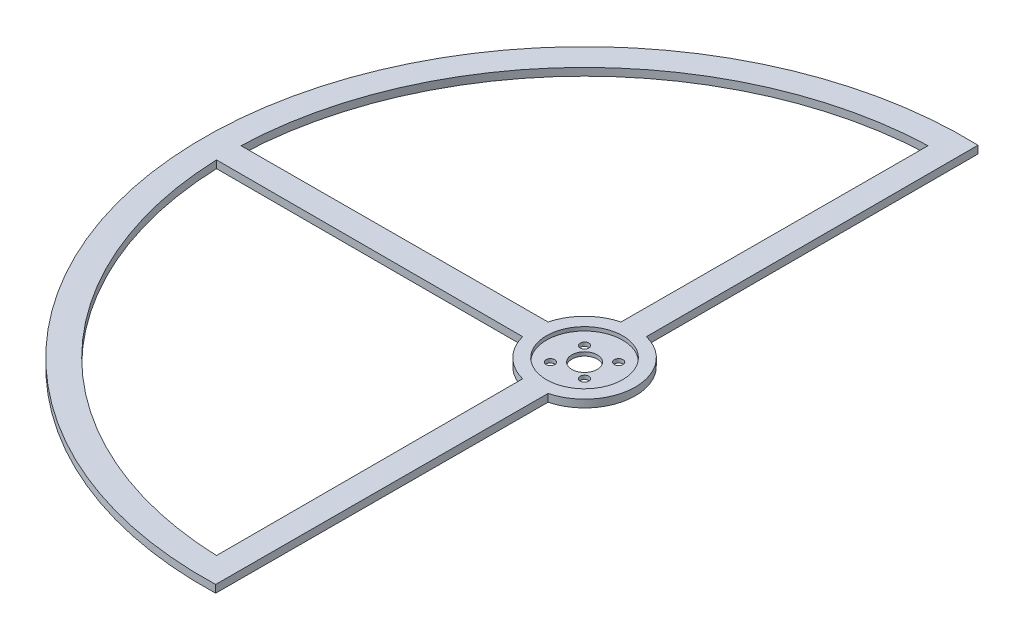
SolidWorks part; units mm, degrees
ref_plane "Front Plane" through (0, 0, 0) normal (0, 0, 1) x (1, 0, 0)
ref_plane "Top Plane" through (0, 0, 0) normal (0, 1, 0) x (1, 0, 0)
ref_plane "Right Plane" through (0, 0, 0) normal (1, 0, 0) x (0, 0, -1)
sketch "Sketch1" plane through (0, 0, 0) normal (0, 1, 0) x (1, 0, 0)
  line L0 (5, -19.3649) -> (4.6875, -149.9267)
  line L1 (5, 19.3649) -> (5, 149.9166)
  line L2 (-5, -19.3649) -> (-5, -139.9107)
  line L4 (-19.3649, -5) -> (-139.9107, -5)
  line L6 (-5, 19.3649) -> (-4.6667, 139.9222)
  line L7 (-19.3649, 5) -> (-139.9222, 4.6667)
  arc A0 (-5, 19.3649) -> (-19.3649, 5) centre (0, 0) ccw
  circle A1 centre (0, 0) radius 5
  circle A2 centre (-5.6569, 5.6569) radius 1.7
  circle A3 centre (5.6569, -5.6569) radius 1.7
  circle A4 centre (6.7175, 6.7175) radius 1.7
  circle A5 centre (-6.7175, -6.7175) radius 1.7
  arc A6 (5, 149.9166) -> (4.6875, -149.9267) centre (0, 0) ccw
  arc A7 (-4.6667, 139.9222) -> (-139.9222, 4.6667) centre (0, 0) ccw
  arc A8 (-19.3649, -5) -> (-5, -19.3649) centre (0, 0) ccw
  arc A9 (5, -19.3649) -> (5, 19.3649) centre (0, 0) ccw
  arc A10 (-139.9107, -5) -> (-5, -139.9107) centre (0, 0) ccw
  dimension "D2" = 10
  dimension "D3" = 40
extrude "Boss-Extrude1" add sketch "Sketch1" along normal blind 3
sketch "Sketch2" plane through (0, 3, 0) normal (0, 1, 0) x (1, 0, 0)
  circle A0 centre (0, 0) radius 15
extrude "Cut-Extrude1" cut sketch "Sketch2" against normal blind 1.5
